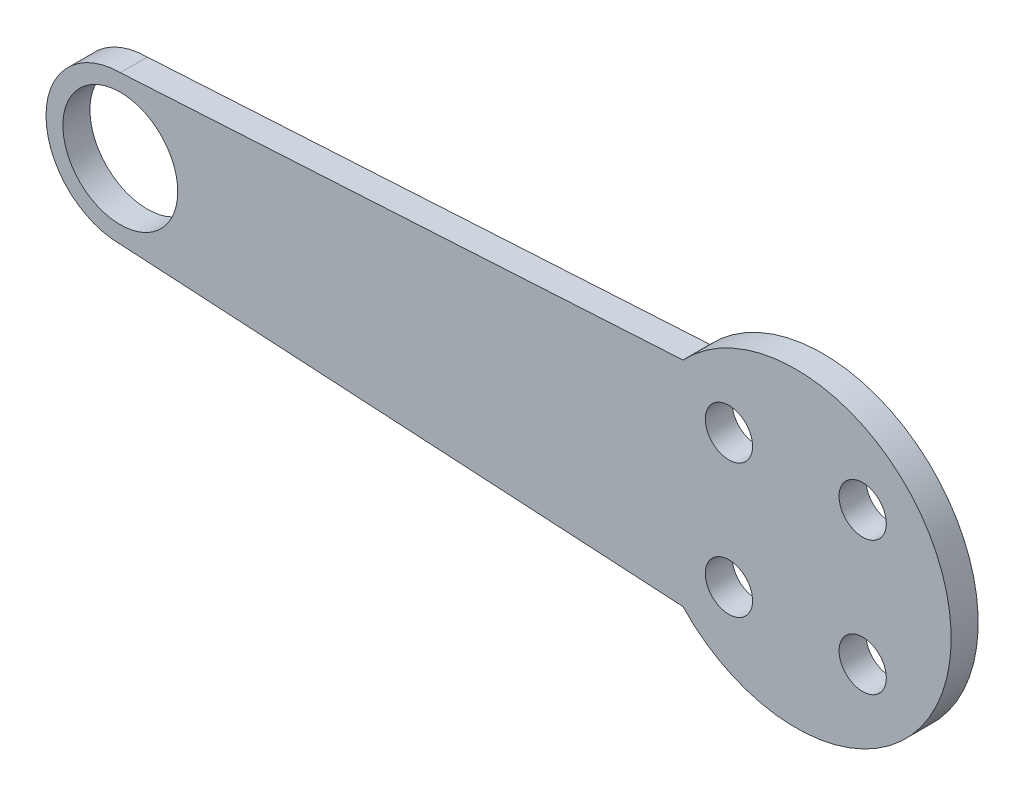
SolidWorks part; units mm, degrees
ref_plane "前视基准面" through (0, 0, 0) normal (0, 0, 1) x (1, 0, 0)
ref_plane "上视基准面" through (0, 0, 0) normal (0, 1, 0) x (1, 0, 0)
ref_plane "右视基准面" through (0, 0, 0) normal (1, 0, 0) x (0, 0, -1)
sketch "草图1" plane through (0, 0, 0) normal (0, 0, 1) x (1, 0, 0)
  line L0 (0, 0) -> (-50, 0) construction
  line L1 (-50, 5.5) -> (-8.3544, 7.9028)
  line L2 (-50, -5.5) -> (-8.3544, -7.9028)
  line L3 (4.9497, -4.9497) -> (4.9497, 4.9497) construction
  line L4 (4.9497, -4.9497) -> (-4.9497, -4.9497) construction
  line L5 (4.9497, -4.9497) -> (4.9497, 4.9497) construction
  line L6 (4.9497, 4.9497) -> (-4.9497, 4.9497) construction
  line L7 (-4.9497, -4.9497) -> (-4.9497, 4.9497) construction
  line L8 (4.9497, -4.9497) -> (-4.9497, 4.9497) construction
  line L9 (4.9497, 4.9497) -> (-4.9497, -4.9497) construction
  line L10 (-4.9497, -4.9497) -> (4.9497, -4.9497) construction
  line L11 (-4.9497, 4.9497) -> (-4.9497, -4.9497) construction
  arc A0 (-8.3544, -7.9028) -> (-8.3544, 7.9028) centre (0, 0) ccw
  arc A1 (-50, 5.5) -> (-50, -5.5) centre (-50, 0) ccw
  circle A2 centre (-50, 0) radius 4.25
  circle A3 centre (4.9497, 4.9497) radius 1.75
  circle A4 centre (4.9497, -4.9497) radius 1.75
  circle A5 centre (-4.9497, -4.9497) radius 1.75
  circle A6 centre (-4.9497, 4.9497) radius 1.75
  point P27 (0, 0)
  dimension "D1" = 23
  dimension "D2" = 11
  dimension "D4" = 8.5
  dimension "D7" = 3.5
  dimension "D3" = 50
  dimension "D5" = 90
  dimension "D6" = 14
  dimension "D8" = 4
extrude "凸台-拉伸1" add sketch "草图1" along normal blind 2 contours L1 A0 L2 A1 | A2 | A3 | A6 | A4 | A5
